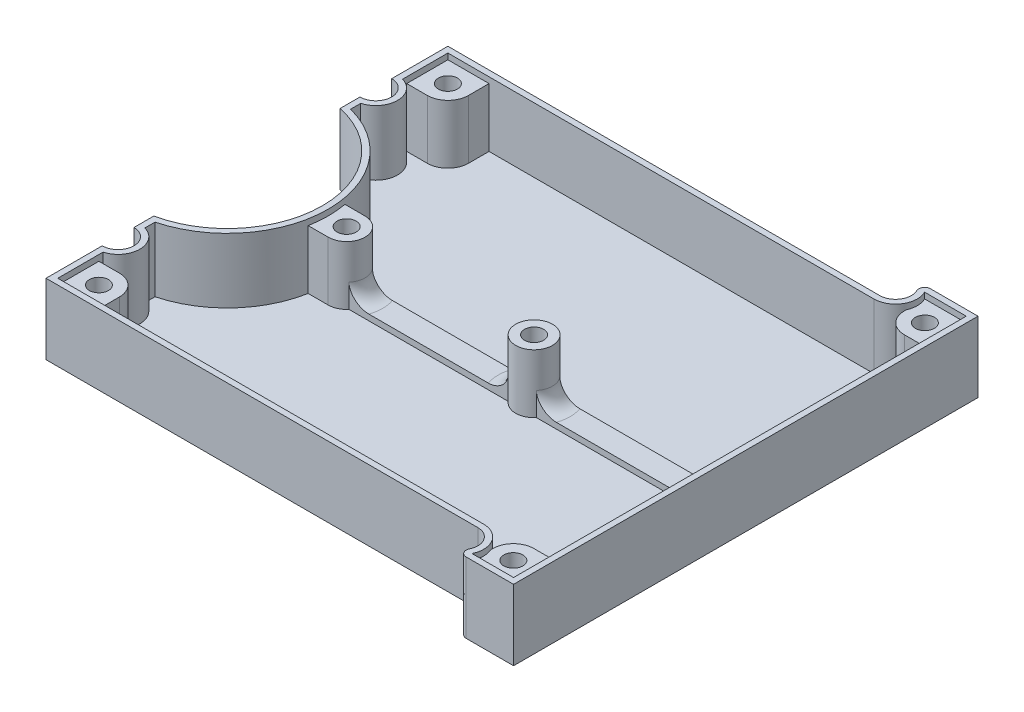
SolidWorks part; units mm, degrees
ref_plane "Front Plane" through (0, 0, 0) normal (0, 0, 1) x (1, 0, 0)
ref_plane "Top Plane" through (0, 0, 0) normal (0, 1, 0) x (1, 0, 0)
ref_plane "Right Plane" through (0, 0, 0) normal (1, 0, 0) x (0, 0, -1)
sketch "Sketch1" plane through (0, 0, 0) normal (0, 1, 0) x (1, 0, 0)
  line L0 (0, 30.3854) -> (0, -26.0557) construction
  line L1 (-19.0199, 0) -> (15.6179, 0) construction
  line L2 (-73.452, 57.1764) -> (-73.452, -39.7909) construction
  line L3 (0, 34.18) -> (-73.452, 34.18)
  line L4 (-73.452, 34.18) -> (-73.452, 24.62)
  line L5 (-73.452, 19.22) -> (-73.452, 15.8456)
  line L6 (0, -34.18) -> (-73.452, -34.18)
  line L7 (-73.452, -34.18) -> (-73.452, -24.62)
  line L8 (-73.452, -19.22) -> (-73.452, -15.8456)
  line L9 (11.4, 39.5) -> (11.4, -39.5)
  line L10 (11.4, 39.5) -> (0.6524, 39.5)
  line L11 (11.4, -39.5) -> (0.6524, -39.5)
  circle A0 centre (0, 36.88) radius 2.5
  circle A1 centre (0, -36.88) radius 2.5
  circle A2 centre (-73.452, 21.92) radius 2.5
  circle A3 centre (-73.452, -21.92) radius 2.5
  circle A4 centre (-76.822, 0) radius 16
  circle A5 centre (-73.452, 21.92) radius 2.7
  circle A6 centre (-76.822, 0) radius 16.2
  circle A7 centre (-73.452, -21.92) radius 2.7
  circle A8 centre (0, 36.88) radius 2.7
  circle A9 centre (0, -36.88) radius 2.7
  point P39 (11.4, 0)
  dimension "D2" = 5
  dimension "D3" = 43.84
  dimension "D5" = 32
  dimension "D1" = 73.76
  dimension "D4" = 74.96
  dimension "D6" = 3.37
  dimension "D12" = 79
  dimension "D13" = 11.4
  dimension "D7" = 0.2
  dimension "D8" = 0.2
  dimension "D9" = 0.2
  dimension "D10" = 0.2
  dimension "D11" = 0.2
extrude "Base shape" add sketch "Sketch1" along normal blind 12 contours L6 A9 L11 L9 L10 A8 L3 L4 A5 L5 A6 L8 A7 L7
fillet "Fillets" radius 1 2 edges at (0.6524, 6, -39.5) (0.6524, 6, 39.5)
sketch "Sketch2" plane through (0, 12, 0) normal (0, 1, 0) x (1, 0, 0)
  line L18 (10.4, 38.5) -> (3.3265, 38.5)
  line L19 (0, 33.18) -> (-72.452, 33.18)
  line L20 (-72.452, 33.18) -> (-72.452, 25.4823)
  line L21 (-72.452, 18.3577) -> (-72.452, 16.6356)
  line L22 (-72.452, -16.6356) -> (-72.452, -18.3577)
  line L23 (-72.452, -25.4823) -> (-72.452, -33.18)
  line L24 (-72.452, -33.18) -> (0, -33.18)
  line L25 (3.3265, -38.5) -> (10.4, -38.5)
  line L26 (10.4, -38.5) -> (10.4, 38.5)
  line L27 (10.4, 38.5) -> (3.3265, 38.5)
  line L28 (0, 33.18) -> (-72.452, 33.18)
  line L29 (-72.452, 33.18) -> (-72.452, 25.4823)
  line L30 (-72.452, 18.3577) -> (-72.452, 16.6356)
  line L31 (-72.452, -16.6356) -> (-72.452, -18.3577)
  line L32 (-72.452, -25.4823) -> (-72.452, -33.18)
  line L33 (-72.452, -33.18) -> (0, -33.18)
  line L34 (3.3265, -38.5) -> (10.4, -38.5)
  line L35 (10.4, -38.5) -> (10.4, 38.5)
  arc A15 (0, 33.18) -> (3.3265, 38.5) centre (0, 36.88) ccw
  arc A16 (-72.452, 18.3577) -> (-72.452, 25.4823) centre (-73.452, 21.92) ccw
  arc A17 (-72.452, -16.6356) -> (-72.452, 16.6356) centre (-76.822, 0) ccw
  arc A18 (-72.452, -25.4823) -> (-72.452, -18.3577) centre (-73.452, -21.92) ccw
  arc A19 (3.3265, -38.5) -> (0, -33.18) centre (0, -36.88) ccw
  arc A22 (0, 33.18) -> (3.3265, 38.5) centre (0, 36.88) ccw
  arc A23 (-72.452, 18.3577) -> (-72.452, 25.4823) centre (-73.452, 21.92) ccw
  arc A24 (-72.452, -16.6356) -> (-72.452, 16.6356) centre (-76.822, 0) ccw
  arc A25 (-72.452, -25.4823) -> (-72.452, -18.3577) centre (-73.452, -21.92) ccw
  arc A26 (3.3265, -38.5) -> (0, -33.18) centre (0, -36.88) ccw
  point P6 (-67.4824, 28.8613)
  dimension "D1" = 1
extrude "Inside cut" cut sketch "Sketch2" against normal offset from surface (11 mm away) 1 up to face at (-33.3577, 0, 0)
sketch "Sketch3" plane through (0, 1, 0) normal (0, 1, 0) x (1, 0, 0)
  line L0 (0, 33.18) -> (-72.452, 33.18) construction
  line L1 (-72.452, 25.4823) -> (-72.452, 33.18) construction
  line L2 (-68.952, 26.18) -> (-72.452, 26.18)
  line L3 (-65.452, 29.68) -> (-65.452, 33.18)
  line L4 (-72.452, 33.18) -> (0, 33.18) construction
  line L5 (-13.3719, 0) -> (5.5751, 0) construction
  line L6 (-65.452, -29.68) -> (-65.452, -33.18)
  line L7 (-68.952, -26.18) -> (-72.452, -26.18)
  line L8 (6.8632, 38.5) -> (6.8632, -38.5) construction
  line L9 (10.4, 38.5) -> (3.3265, 38.5) construction
  line L10 (10.4, -38.5) -> (3.3265, -38.5) construction
  line L12 (0, 33.18) -> (3.8737, 33.18)
  line L13 (6.8632, 31.5) -> (10.4, 31.5)
  line L14 (10.4, 38.5) -> (10.4, -38.5) construction
  line L15 (6.8632, -31.5) -> (10.4, -31.5)
  line L16 (0, -33.18) -> (3.8737, -33.18)
  line L17 (-56.497, 3.125) -> (-59.9083, 3.125)
  line L18 (-56.497, -3.125) -> (-59.9083, -3.125)
  line L19 (-59.622, 0) -> (10.4, 0) construction
  line L26 (10.4, -38.5) -> (10.4, 38.5)
  line L27 (10.4, 38.5) -> (3.3265, 38.5)
  line L28 (0, 33.18) -> (-72.452, 33.18)
  line L29 (-72.452, 33.18) -> (-72.452, 25.4823)
  line L30 (-72.452, 18.3577) -> (-72.452, 16.6356)
  line L31 (-72.452, -16.6356) -> (-72.452, -18.3577)
  line L32 (-72.452, -25.4823) -> (-72.452, -33.18)
  line L33 (-72.452, -33.18) -> (0, -33.18)
  line L34 (3.3265, -38.5) -> (10.4, -38.5)
  line L35 (10.4, -38.5) -> (10.4, 38.5)
  line L36 (10.4, 38.5) -> (3.3265, 38.5)
  line L37 (0, 33.18) -> (-72.452, 33.18)
  line L38 (-72.452, 33.18) -> (-72.452, 25.4823)
  line L39 (-72.452, 18.3577) -> (-72.452, 16.6356)
  line L40 (-72.452, -16.6356) -> (-72.452, -18.3577)
  line L41 (-72.452, -25.4823) -> (-72.452, -33.18)
  line L42 (-72.452, -33.18) -> (0, -33.18)
  line L43 (3.3265, -38.5) -> (10.4, -38.5)
  circle A0 centre (-68.952, 29.68) radius 1.625
  circle A1 centre (-68.952, 29.68) radius 3.5
  circle A2 centre (-68.952, -29.68) radius 1.625
  circle A3 centre (-68.952, -29.68) radius 3.5
  circle A4 centre (6.8632, 35) radius 1.625
  circle A5 centre (6.8632, 35) radius 3.5
  circle A6 centre (6.8632, -35) radius 1.625
  circle A7 centre (6.8632, -35) radius 3.5
  circle A8 centre (-56.497, 0) radius 1.625
  circle A9 centre (-56.497, 0) radius 3.125
  circle A10 centre (-24.611, 0) radius 3.125
  circle A11 centre (-24.611, 0) radius 1.625
  arc A16 (0, 33.18) -> (3.3265, 38.5) centre (0, 36.88) ccw
  arc A17 (-72.452, 18.3577) -> (-72.452, 25.4823) centre (-73.452, 21.92) ccw
  arc A18 (-72.452, -16.6356) -> (-72.452, 16.6356) centre (-76.822, 0) ccw
  arc A19 (-72.452, -25.4823) -> (-72.452, -18.3577) centre (-73.452, -21.92) ccw
  arc A20 (3.3265, -38.5) -> (0, -33.18) centre (0, -36.88) ccw
  arc A23 (0, 33.18) -> (3.3265, 38.5) centre (0, 36.88) ccw
  arc A24 (-72.452, 18.3577) -> (-72.452, 25.4823) centre (-73.452, 21.92) ccw
  arc A25 (-72.452, -16.6356) -> (-72.452, 16.6356) centre (-76.822, 0) ccw
  arc A26 (-72.452, -25.4823) -> (-72.452, -18.3577) centre (-73.452, -21.92) ccw
  arc A27 (3.3265, -38.5) -> (0, -33.18) centre (0, -36.88) ccw
  point P77 (-18.3545, 0)
  dimension "D1" = 3.25
  dimension "D2" = 7
  dimension "D4" = 6.25
  dimension "D3" = 0
extrude "Mounting posts" add sketch "Sketch3" along normal offset from surface (10 mm away) 1
sketch "Sketch4" plane through (0, 1, 0) normal (0, 1, 0) x (1, 0, 0)
  line L0 (10.4, 31.5) -> (10.4, -31.5) construction
  line L1 (-59.622, 2) -> (10.4, 2)
  line L2 (-59.622, 2) -> (-59.622, -2)
  line L3 (-59.622, -2) -> (10.4, -2)
  line L4 (10.4, 2) -> (10.4, -2)
  line L5 (-59.622, 2) -> (10.4, -2) construction
  line L6 (-59.622, -2) -> (10.4, 2) construction
  line L22 (-59.9083, 3.125) -> (-56.497, 3.125)
  line L23 (-56.497, -3.125) -> (-59.9083, -3.125)
  line L24 (-72.452, -16.6356) -> (-72.452, -18.3577)
  line L25 (-72.452, -25.4823) -> (-72.452, -26.18)
  line L26 (-72.452, -26.18) -> (-68.952, -26.18)
  line L27 (-65.452, -29.68) -> (-65.452, -33.18)
  line L28 (-65.452, -33.18) -> (0, -33.18)
  line L29 (6.8632, -31.5) -> (10.4, -31.5)
  line L30 (10.4, -31.5) -> (10.4, 31.5)
  line L31 (10.4, 31.5) -> (6.8632, 31.5)
  line L32 (0, 33.18) -> (-65.452, 33.18)
  line L33 (-65.452, 33.18) -> (-65.452, 29.68)
  line L34 (-68.952, 26.18) -> (-72.452, 26.18)
  line L35 (-72.452, 26.18) -> (-72.452, 25.4823)
  line L36 (-72.452, 18.3577) -> (-72.452, 16.6356)
  line L37 (-59.9083, 3.125) -> (-56.497, 3.125)
  line L38 (-56.497, -3.125) -> (-59.9083, -3.125)
  line L39 (-72.452, -16.6356) -> (-72.452, -18.3577)
  line L40 (-72.452, -25.4823) -> (-72.452, -26.18)
  line L41 (-72.452, -26.18) -> (-68.952, -26.18)
  line L42 (-65.452, -29.68) -> (-65.452, -33.18)
  line L43 (-65.452, -33.18) -> (0, -33.18)
  line L44 (6.8632, -31.5) -> (10.4, -31.5)
  line L45 (10.4, -31.5) -> (10.4, 31.5)
  line L46 (10.4, 31.5) -> (6.8632, 31.5)
  line L47 (0, 33.18) -> (-65.452, 33.18)
  line L48 (-65.452, 33.18) -> (-65.452, 29.68)
  line L49 (-68.952, 26.18) -> (-72.452, 26.18)
  line L50 (-72.452, 26.18) -> (-72.452, 25.4823)
  line L51 (-72.452, 18.3577) -> (-72.452, 16.6356)
  arc A11 (-59.9083, 3.125) -> (-72.452, 16.6356) centre (-76.822, 0) ccw
  arc A12 (-56.497, -3.125) -> (-56.497, 3.125) centre (-56.497, 0) ccw
  arc A13 (-72.452, -16.6356) -> (-59.9083, -3.125) centre (-76.822, 0) ccw
  arc A14 (-72.452, -25.4823) -> (-72.452, -18.3577) centre (-73.452, -21.92) ccw
  arc A15 (-65.452, -29.68) -> (-68.952, -26.18) centre (-68.952, -29.68) ccw
  arc A16 (3.3845, -35.3849) -> (0, -33.18) centre (0, -36.88) ccw
  arc A17 (6.8632, -31.5) -> (3.3845, -35.3849) centre (6.8632, -35) ccw
  arc A18 (3.3845, 35.3849) -> (6.8632, 31.5) centre (6.8632, 35) ccw
  arc A19 (0, 33.18) -> (3.3845, 35.3849) centre (0, 36.88) ccw
  arc A20 (-68.952, 26.18) -> (-65.452, 29.68) centre (-68.952, 29.68) ccw
  arc A21 (-72.452, 18.3577) -> (-72.452, 25.4823) centre (-73.452, 21.92) ccw
  arc A22 (-59.9083, 3.125) -> (-72.452, 16.6356) centre (-76.822, 0) ccw
  arc A23 (-56.497, -3.125) -> (-56.497, 3.125) centre (-56.497, 0) ccw
  arc A24 (-72.452, -16.6356) -> (-59.9083, -3.125) centre (-76.822, 0) ccw
  arc A25 (-72.452, -25.4823) -> (-72.452, -18.3577) centre (-73.452, -21.92) ccw
  arc A26 (-65.452, -29.68) -> (-68.952, -26.18) centre (-68.952, -29.68) ccw
  arc A27 (3.3845, -35.3849) -> (0, -33.18) centre (0, -36.88) ccw
  arc A28 (6.8632, -31.5) -> (3.3845, -35.3849) centre (6.8632, -35) ccw
  arc A29 (3.3845, 35.3849) -> (6.8632, 31.5) centre (6.8632, 35) ccw
  arc A30 (0, 33.18) -> (3.3845, 35.3849) centre (0, 36.88) ccw
  arc A31 (-68.952, 26.18) -> (-65.452, 29.68) centre (-68.952, 29.68) ccw
  arc A32 (-72.452, 18.3577) -> (-72.452, 25.4823) centre (-73.452, 21.92) ccw
  point P0 (-24.611, 0)
  circle M5 centre (-24.611, 0) radius 3.125
  arc M8 (-56.497, 3.125) -> (-56.497, -3.125) centre (-56.497, 0) cw
  line M21 (10.4, -31.5) -> (10.4, 31.5)
  dimension "D1" = 4
  dimension "D2" = 0
extrude "Center reinforcement" add sketch "Sketch4" along normal blind 1 contours L3 L1 M8 M5 | L3 L1 M5 M21
fillet "Reinforcement fillets" radius 3 4 edges at (10.4, 2, 0) (-53.372, 2, 0) (-21.486, 2, 0) (-27.736, 2, 0)
